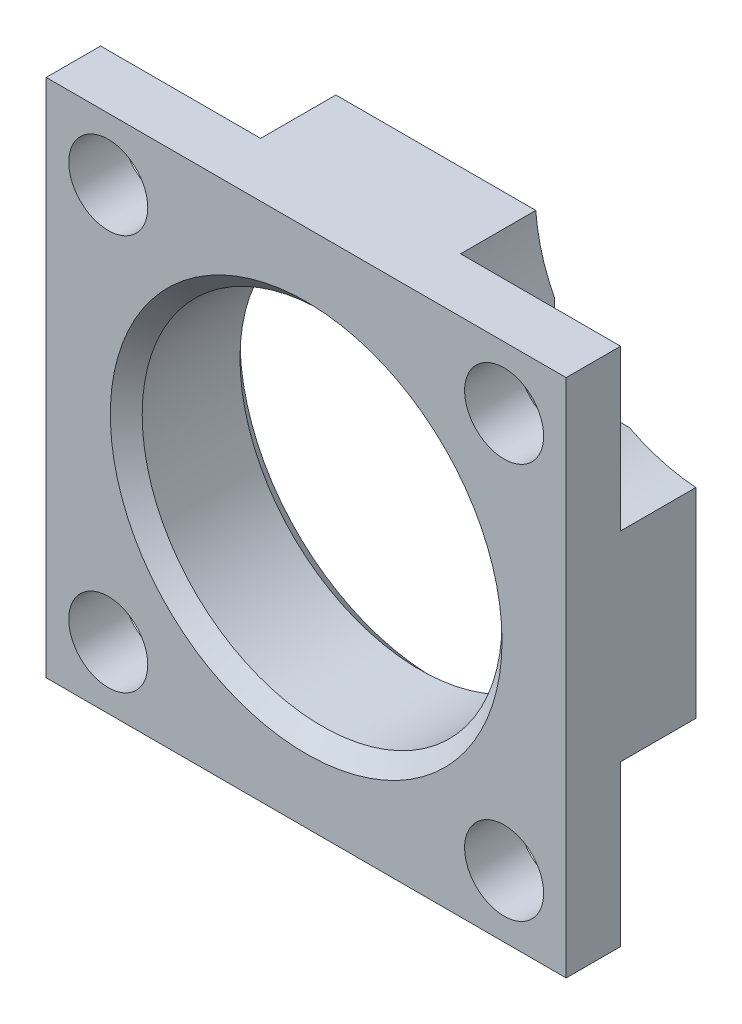
SolidWorks part; units mm, degrees
material "Alloy Steel"
ref_plane "Front Plane" through (0, 0, 0) normal (0, 0, 1) x (1, 0, 0)
ref_plane "Top Plane" through (0, 0, 0) normal (0, 1, 0) x (1, 0, 0)
ref_plane "Right Plane" through (0, 0, 0) normal (1, 0, 0) x (0, 0, -1)
sketch "Sketch1" plane through (0, 0, 0) normal (0, 0, 1) x (1, 0, 0)
  line L0 (19.05, 19.05) -> (-19.05, -19.05) construction
  line L1 (-19.05, 19.05) -> (19.05, 19.05)
  line L2 (-19.05, 19.05) -> (-19.05, -19.05)
  line L3 (-19.05, -19.05) -> (19.05, -19.05)
  line L4 (19.05, 19.05) -> (19.05, -19.05)
  line L5 (-19.05, 19.05) -> (19.05, -19.05) construction
  circle A0 centre (0, 0) radius 13.183
  dimension "D3" = 26.366
  dimension "D1" = 38.1
  dimension "D2" = 38.1
extrude "Extrude1" add sketch "Sketch1" against normal blind 9.4996
sketch "Sketch2" plane through (0, 0, -9.4996) normal (0, 0, -1) x (1, 0, 0)
  line L1 (19.05, 19.05) -> (19.05, -19.05) construction
  line L3 (19.05, 19.05) -> (19.05, 7.3246)
  line L4 (0, 0) -> (-25.3528, 0) construction
  line L5 (0, 0) -> (0, 27.5861) construction
  line L6 (19.05, -19.05) -> (19.05, -7.3246)
  line L7 (-19.05, -19.05) -> (-7.3246, -19.05)
  line L8 (-19.05, 19.05) -> (-7.3246, 19.05)
  line L9 (-19.05, -19.05) -> (-19.05, -7.3246)
  line L10 (-19.05, 19.05) -> (-19.05, 7.3246)
  line L11 (7.3246, 19.05) -> (19.05, 19.05)
  line L12 (7.3246, -19.05) -> (19.05, -19.05)
  arc A0 (19.05, -7.3246) -> (7.3246, -19.05) centre (19.9898, -19.9898) ccw
  arc A1 (19.05, 7.3246) -> (7.3246, 19.05) centre (19.9898, 19.9898) cw
  arc A2 (-19.05, 7.3246) -> (-7.3246, 19.05) centre (-19.9898, 19.9898) ccw
  arc A3 (-19.05, -7.3246) -> (-7.3246, -19.05) centre (-19.9898, -19.9898) cw
  dimension "D1" = 12.7
  dimension "D2" = 19.9898
  dimension "D3" = 19.9898
extrude "Cut-Extrude1" cut sketch "Sketch2" against normal blind 5.5118
hole_wizard "Hole1" positions "Sketch4" profile "Sketch3" legacy end condition up to next
sketch "Sketch4" plane through (0, 0, -3.9878) normal (0, 0, -1) x (-1, 0, 0)
  point P0 (14.5034, 14.5034)
  point P6 (14.5034, -14.5034)
  point P9 (-14.5034, 14.5034)
  point P11 (-14.5034, -14.5034)
  dimension "D1" = 14.5034
  dimension "D2" = 14.5034
  dimension "D3" = 29.0068
  dimension "D4" = 29.0068
sketch "Sketch3" plane through (-14.5034, 14.5034, -3.9878) normal (1, 0, 0) x (0, 1, 0)
  line L0 (0, 0) -> (0, 3.9878)
  line L1 (0, 3.9878) -> (2.8956, 3.9878)
  line L2 (2.8956, 3.9878) -> (2.8956, 0)
  line L3 (2.8956, 0) -> (0, 0)
  line L4 (0, 110) -> (0, -10) construction
  dimension "Diameter" = 5.7912
  dimension "Depth" = 3.9878
sketch "Sketch5" plane through (0, 0, 0) normal (1, 0, 0) x (0, 0, -1)
  line L0 (-7.3809, 0) -> (17.6409, 0) construction
  line L1 (9.4996, 7.3246) -> (9.4996, 19.05) construction
  line L4 (9.4996, 13.183) -> (0, 13.183) construction
  line L5 (9.4996, 13.183) -> (9.4996, 14.351)
  line L7 (9.4996, 13.183) -> (8.3316, 13.183)
  line L8 (9.4996, 14.351) -> (8.3316, 13.183)
  line L9 (1.168, 13.183) -> (0, 13.183)
  line L10 (0, 13.183) -> (0, 14.351)
  line L11 (0, -19.05) -> (0, 19.05) construction
  line L12 (0, 14.351) -> (1.168, 13.183)
  dimension "D1" = 28.702
  dimension "D2" = 45
revolve "Cut-Revolve1" cut sketch "Sketch5" angle 360 about L0
sketch "Sketch6" plane through (0, 0, 0) normal (0, 1, 0) x (1, 0, 0)
  line L0 (0, 0) -> (0, 13.4089) construction
  line L1 (15.875, 9.4996) -> (16.256, 9.1186)
  line L2 (19.05, 9.4996) -> (7.3246, 9.4996) construction
  line L3 (16.256, 9.1186) -> (16.637, 9.4996)
  line L4 (16.637, 9.4996) -> (15.875, 9.4996)
  dimension "D1" = 90
  dimension "D2" = 45
  dimension "D3" = 32.512
  dimension "D4" = 0.762
revolve "Cut-Revolve2" cut sketch "Sketch6" angle 360 about L0
